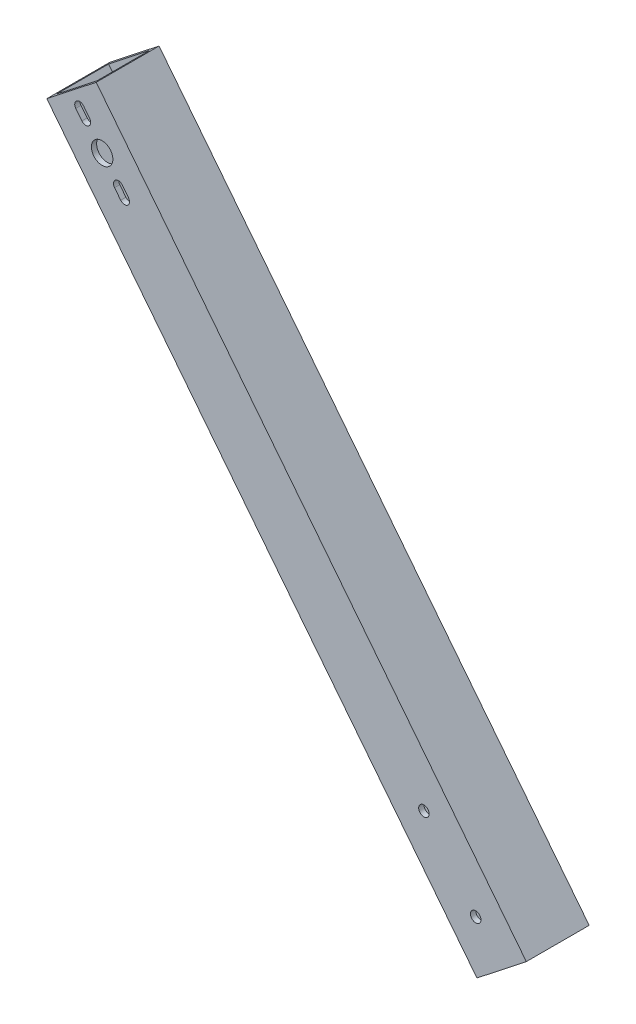
SolidWorks part; units mm, degrees
material "1060 Alloy"
ref_plane "Front Plane" through (0, 0, 0) normal (0, 0, 1) x (1, 0, 0)
ref_plane "Top Plane" through (0, 0, 0) normal (0, 1, 0) x (1, 0, 0)
ref_plane "Right Plane" through (0, 0, 0) normal (1, 0, 0) x (0, 0, -1)
sketch "Sketch1" plane through (0, 0, 0) normal (0, 0, 1) x (1, 0, 0)
  line L0 (-220.5703, 200.6607) -> (-205.601, 212.443)
  line L1 (-220.5703, 200.6607) -> (-90.1802, 35)
  line L2 (-205.601, 212.443) -> (-75.2108, 46.7822)
  line L3 (-90.1802, 35) -> (-75.2108, 46.7822)
  dimension "D1" = 35
  dimension "D2" = 19.05
  dimension "D3" = 210.82
extrude "Boss-Extrude1" add sketch "Sketch1" along normal blind 19.05 contours L2 L3 L1 L0
shell "Shell1" thickness 1.5875
sketch "Sketch2" plane through (-181.897, 231.1002, 0) normal (-0.6185, 0.7858, 0) x (0.7858, 0.6185, 0)
  line L0 (-49.2157, 0) -> (-30.1657, 0) construction
  line L1 (-47.6282, -1.5875) -> (-31.7532, -1.5875)
  line L2 (-47.6282, -1.5875) -> (-47.6282, -17.4625)
  line L3 (-47.6282, -17.4625) -> (-31.7532, -17.4625)
  line L4 (-31.7532, -1.5875) -> (-31.7532, -17.4625)
  line L5 (-47.6282, -1.5875) -> (-31.7532, -17.4625) construction
  line L6 (-47.6282, -17.4625) -> (-31.7532, -1.5875) construction
  line L7 (-30.1657, -19.05) -> (-30.1657, 0) construction
  line L8 (-49.2157, -19.05) -> (-49.2157, 0) construction
  point P0 (-39.6907, -9.525)
  point P5 (-39.6907, 0)
  point P6 (-30.1657, -9.525)
  dimension "D1" = 1.5875
  dimension "D2" = 1.5875
extrude "Cut-Extrude1" cut sketch "Sketch2" against normal through all
sketch "Sketch3" plane through (0, 0, 19.05) normal (0, 0, 1) x (1, 0, 0)
  line L0 (-205.601, 212.443) -> (-75.2108, 46.7822) construction
  line L1 (-220.5703, 200.6607) -> (-205.601, 212.443) construction
  line L2 (-213.0856, 206.5519) -> (-203.8079, 194.7645) construction
  circle A0 centre (-203.8079, 194.7645) radius 3.25
  dimension "D2" = 15.0006
extrude "Cut-Extrude2" cut sketch "Sketch3" against normal blind 2.54 contours A0
sketch "Sketch7" plane through (0, 0, 19.05) normal (0, 0, 1) x (1, 0, 0)
  line L0 (-213.0856, 206.5519) -> (-82.6955, 40.8911) construction
  line L1 (-220.5703, 200.6607) -> (-205.601, 212.443) construction
  line L2 (-90.1802, 35) -> (-75.2108, 46.7822) construction
  circle A0 centre (-106.26, 70.8298) radius 1.5875
  circle A1 centre (-90.5503, 50.8707) radius 1.5875
  dimension "D1" = 3.175
  dimension "D2" = 3.175
  dimension "D3" = 25.4
  dimension "D4" = 12.7
extrude "Cut-Extrude3" cut sketch "Sketch7" against normal through all
sketch "Sketch9" plane through (0, 0, 19.05) normal (0, 0, 1) x (1, 0, 0)
  line L0 (-198.86, 188.4781) -> (-197.0045, 186.1208) construction
  line L1 (-197.6813, 189.4059) -> (-195.8258, 187.0485)
  line L2 (-200.0387, 187.5504) -> (-198.1832, 185.193)
  line L3 (-210.6113, 203.4082) -> (-208.7558, 201.0508) construction
  line L4 (-209.4326, 204.3359) -> (-207.5771, 201.9786)
  line L5 (-211.79, 202.4805) -> (-209.9345, 200.1231)
  line L6 (-220.5703, 200.6607) -> (-90.1802, 35) construction
  line L7 (-208.7558, 201.0508) -> (-198.86, 188.4781) construction
  arc A0 (-197.6813, 189.4059) -> (-200.0387, 187.5504) centre (-198.86, 188.4781) ccw
  arc A1 (-198.1832, 185.193) -> (-195.8258, 187.0485) centre (-197.0045, 186.1208) ccw
  arc A2 (-209.4326, 204.3359) -> (-211.79, 202.4805) centre (-210.6113, 203.4082) ccw
  arc A3 (-209.9345, 200.1231) -> (-207.5771, 201.9786) centre (-208.7558, 201.0508) ccw
  circle A4 centre (-203.8079, 194.7645) radius 3.25 construction
  circle A5 centre (-203.8079, 194.7645) radius 3.25 construction
  point P2 (-197.9322, 187.2995)
  point P7 (-209.6836, 202.2295)
  point P14 (-210.8622, 201.3018)
  point P15 (-208.5049, 203.1572)
  dimension "D1" = 3
  dimension "D2" = 3
  dimension "D3" = 3
  dimension "D4" = 3
  dimension "D5" = 8
extrude "Cut-Extrude4" cut sketch "Sketch9" against normal up to surface (19.05 mm away) up to face at (-88.9628, 50.8707, 0)
